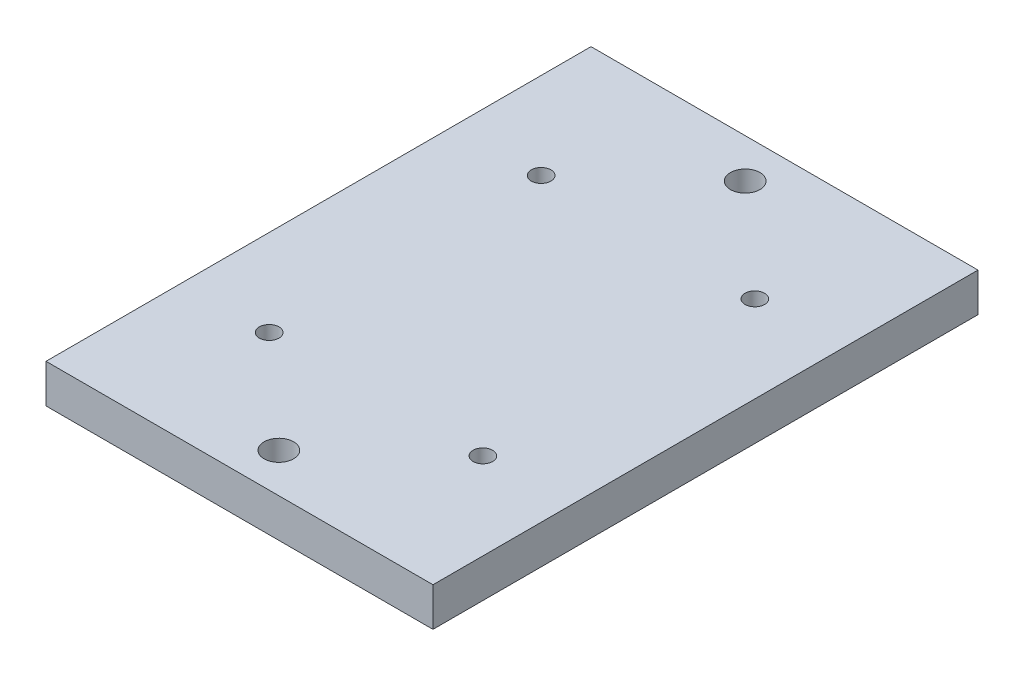
SolidWorks part; units mm, degrees
ref_plane "Front Plane" through (0, 0, 0) normal (0, 0, 1) x (1, 0, 0)
ref_plane "Top Plane" through (0, 0, 0) normal (0, 1, 0) x (1, 0, 0)
ref_plane "Right Plane" through (0, 0, 0) normal (1, 0, 0) x (0, 0, -1)
sketch "Sketch2" plane through (0, 0, 0) normal (0, 1, 0) x (1, 0, 0)
  line L1 (0, 0) -> (63.25, 0)
  line L2 (0, 0) -> (0, 89.08)
  line L3 (0, 89.08) -> (63.25, 89.08)
  line L4 (63.25, 0) -> (63.25, 89.08)
extrude "Boss-Extrude1" add sketch "Sketch2" along normal blind 6.32
sketch "Sketch3" plane through (0, 0, 0) normal (0, -1, 0) x (-1, 0, 0)
  circle A0 centre (-31.625, 82.65) radius 2.415
extrude "Cut-Extrude1" cut sketch "Sketch3" against normal blind 6.32
sketch "Sketch4" plane through (0, 0, 0) normal (0, -1, 0) x (-1, 0, 0)
  circle A0 centre (-31.625, 6.43) radius 2.415
extrude "Cut-Extrude2" cut sketch "Sketch4" against normal blind 6.32
sketch "Sketch5" plane through (0, 0, 0) normal (0, -1, 0) x (-1, 0, 0)
  line L1 (-6.265, 12.765) -> (-56.985, 12.765)
  line L2 (-6.265, 12.765) -> (-6.265, 76.315)
  line L3 (-6.265, 76.315) -> (-56.985, 76.315)
  line L4 (-56.985, 12.765) -> (-56.985, 76.315)
  line L5 (-6.265, 12.765) -> (-56.985, 76.315) construction
  line L6 (-6.265, 76.315) -> (-56.985, 12.765) construction
  point P0 (-31.625, 44.54)
extrude "Cut-Extrude3" cut sketch "Sketch5" against normal blind 1.37
fillet "Fillet1" radius 6.35 4 edges at (6.265, 0.685, -76.315) (56.985, 0.685, -76.315) (56.985, 0.685, -12.765) (6.265, 0.685, -12.765)
sketch "Sketch6" plane through (0, 1.37, 0) normal (0, -1, 0) x (-1, 0, 0)
  line L1 (-14.16, 22.315) -> (-49.09, 22.315)
  line L2 (-14.16, 22.315) -> (-14.16, 66.765)
  line L3 (-14.16, 66.765) -> (-49.09, 66.765)
  line L4 (-49.09, 22.315) -> (-49.09, 66.765)
  line L5 (-14.16, 22.315) -> (-49.09, 66.765) construction
  line L6 (-14.16, 66.765) -> (-49.09, 22.315) construction
  point P0 (-31.625, 44.54)
  point P6 (-49.09, 22.315)
  point P7 (-49.09, 66.765)
  point P8 (-14.16, 22.315)
  point P9 (-14.16, 66.765)
sketch "Sketch7" plane through (0, 1.37, 0) normal (0, -1, 0) x (-1, 0, 0)
  circle A0 centre (-49.09, 22.315) radius 1.6
  circle A1 centre (-49.09, 66.765) radius 1.6
  circle A2 centre (-14.16, 66.765) radius 1.6
  circle A3 centre (-14.16, 22.315) radius 1.6
extrude "Cut-Extrude4" cut sketch "Sketch7" against normal through all
